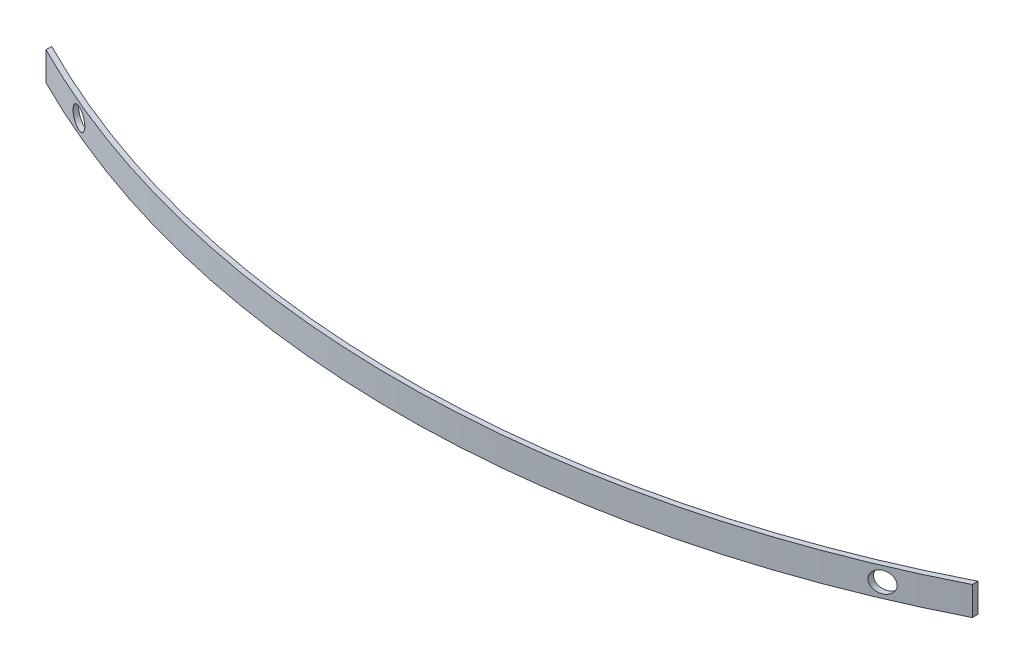
SolidWorks part; units mm, degrees
material "6063-O"
ref_plane "Front Plane" through (0, 0, 0) normal (0, 0, 1) x (1, 0, 0)
ref_plane "Top Plane" through (0, 0, 0) normal (0, 1, 0) x (1, 0, 0)
ref_plane "Right Plane" through (0, 0, 0) normal (1, 0, 0) x (0, 0, -1)
sketch "Sketch1" plane through (0, 0, 0) normal (0, 0, 1) x (1, 0, 0)
  line L0 (0, 0) -> (0, 140)
  line L1 (0, 140) -> (3930, 140)
  line L2 (3930, 140) -> (3930, 0)
  line L3 (3930, 0) -> (0, 0)
  dimension "D1" = 3930
  dimension "D2" = 140
extrude "Boss-Extrude1" add sketch "Sketch1" along normal blind 50
sketch "Sketch2" plane through (0, 0, 50) normal (0, 0, 1) x (1, 0, 0)
  line L0 (3930, 0) -> (3930, 140) construction
  line L1 (0, 140) -> (0, 0) construction
  circle A0 centre (3930, 70) radius 50
  circle A1 centre (0, 70) radius 50
  dimension "D1" = 100
  dimension "D2" = 100
extrude "Cut-Extrude1" cut sketch "Sketch2" against normal blind 50
sketch "Sketch3" plane through (0, 0, 0) normal (0, 0, -1) x (-1, 0, 0)
  line L0 (-3930, 140) -> (-4030, 140)
  line L1 (-4030, 140) -> (-4030, 0)
  line L2 (-4030, 0) -> (-3930, 0)
  line L3 (-3930, 0) -> (-3930, 140)
  line L4 (0, 140) -> (100, 140)
  line L5 (100, 140) -> (100, 0)
  line L6 (100, 0) -> (0, 0)
  line L7 (0, 0) -> (0, 140)
  dimension "D1" = 100
  dimension "D2" = 100
extrude "Boss-Extrude2" add sketch "Sketch3" against normal through all
sketch "Sketch4" plane through (0, 0, 0) normal (0, 0, -1) x (-1, 0, 0)
  line L0 (0, 120) -> (0, 20) construction
  line L1 (-3930, 20) -> (-3930, 120) construction
  circle A0 centre (0, 70) radius 50
  circle A1 centre (-3930, 70) radius 50
extrude "Cut-Extrude2" cut sketch "Sketch4" against normal through all
sketch "Sketch5" plane through (0, 0, 0) normal (0, -1, 0) x (1, 0, 0)
  line L0 (1965, 50) -> (1965, 929.1415) construction
  line L1 (-100, 50) -> (4030, 50) construction
  line L2 (-300, -46.1025) -> (-300, -18.0782)
  line L3 (4230, -46.1025) -> (4230, -18.0782)
  arc A0 (-100, 50) -> (4030, 50) centre (1965, -4503.6551) cw
  arc A1 (-100, 50) -> (-300, -46.1025) centre (1965, -4503.6551) ccw
  arc A2 (4030, 50) -> (4230, -46.1025) centre (1965, -4503.6551) cw
  arc A3 (-110.325, 72.7683) -> (-300, -18.0782) centre (1965, -4503.6551) ccw
  arc A4 (-110.325, 72.7683) -> (4040.325, 72.7683) centre (1965, -4503.6551) cw
  arc A5 (4040.325, 72.7683) -> (4230, -18.0782) centre (1965, -4503.6551) cw
  arc A6 (4040.325, 72.7683) -> (4241.325, -23.8148) centre (1965, -4503.6551) cw construction
  arc A7 (-110.325, 72.7683) -> (-311.325, -23.8148) centre (1965, -4503.6551) ccw construction
  dimension "D1" = 5000
  dimension "D3" = 25
  dimension "D2" = 200
extrude "Boss-Extrude3" add sketch "Sketch5" against normal through all separate body
sketch "Sketch6" plane through (0, 0, 0) normal (0, 0, -1) x (-1, 0, 0)
  circle A0 centre (-3930, 70) radius 50
  circle A1 centre (0, 70) radius 50
extrude "Cut-Extrude3" cut sketch "Sketch6" against normal through all
sketch "Sketch7" plane through (0, 140, 0) normal (0, 1, 0) x (1, 0, 0)
  line L1 (4030, -50) -> (-100, -50)
  line L2 (4030, -50) -> (4030, 0)
  line L3 (4030, 0) -> (-100, 0)
  line L4 (-100, -50) -> (-100, 0)
extrude "Cut-Extrude4" cut sketch "Sketch7" against normal through all
